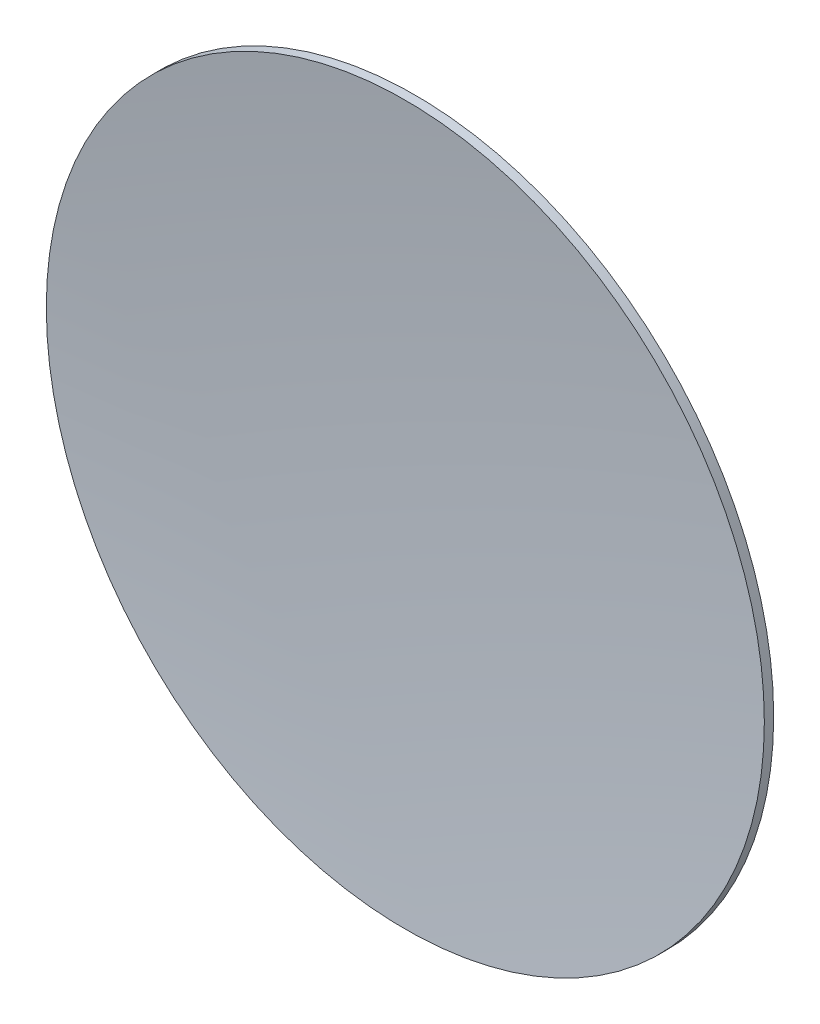
SolidWorks part; units mm, degrees
ref_plane "Front Plane" through (0, 0, 0) normal (0, 0, 1) x (1, 0, 0)
ref_plane "Top Plane" through (0, 0, 0) normal (0, 1, 0) x (1, 0, 0)
ref_plane "Right Plane" through (0, 0, 0) normal (1, 0, 0) x (0, 0, -1)
sketch "Sketch1" plane through (0, 0, 0) normal (0, 0, 1) x (1, 0, 0)
  circle A1 centre (0, 0) radius 19.3
  dimension "D1" = 38.6
extrude "Boss-Extrude1" add sketch "Sketch1" along normal blind 2
sketch "Sketch2" plane through (0, 0, 0) normal (0, 1, 0) x (1, 0, 0)
  line L0 (19.3, 0) -> (-19.3, 0) construction
  line L2 (20.3415, -1.1112) -> (20.3415, 2.0532)
  line L3 (20.3415, 2.0532) -> (0, 2.2717)
  line L4 (0, 2.2717) -> (0, 0)
  line L5 (0, -0.5) -> (0, -3.7743)
  line L6 (0, -3.7743) -> (20.2782, -3.7743)
  line L7 (20.2782, -3.7743) -> (20.287, -1.6082)
  arc A0 (0, 0) -> (20.3415, -1.1112) centre (0, -186.745) cw
  arc A1 (0, -0.5) -> (20.287, -1.6082) centre (0, -186.745) cw
  dimension "D1" = 0.5
revolve "Cut-Revolve1" cut sketch "Sketch2" angle 360 about L4
